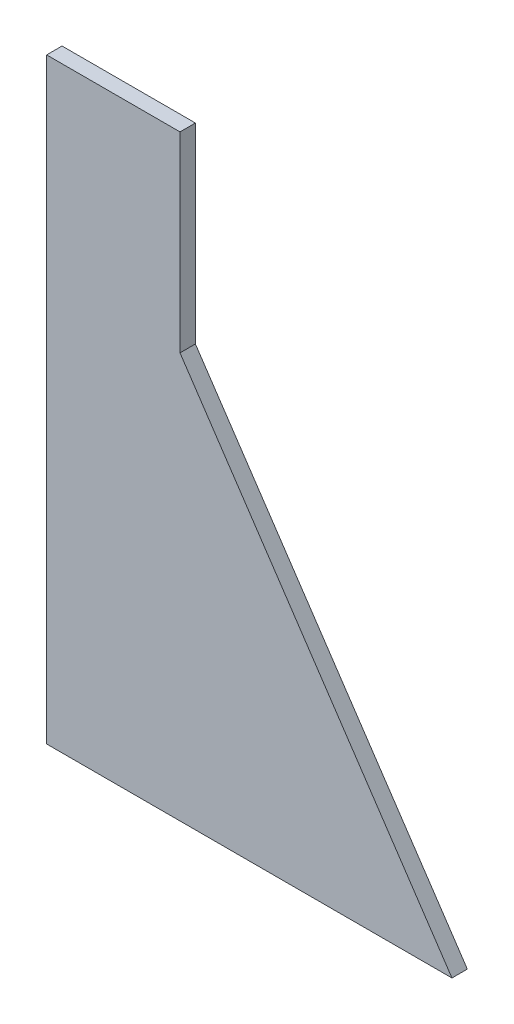
SolidWorks part; units mm, degrees
ref_plane "Front Plane" through (0, 0, 0) normal (0, 0, 1) x (1, 0, 0)
ref_plane "Top Plane" through (0, 0, 0) normal (0, 1, 0) x (1, 0, 0)
ref_plane "Right Plane" through (0, 0, 0) normal (1, 0, 0) x (0, 0, -1)
ref_plane "Plane1" through (0, 0, -231.834) normal (0, 0, -1) x (0, -1, 0)
sketch "Sketch1" plane through (0, 0, -231.834) normal (0, 0, 1) x (1, 0, 0)
  line L0 (0, 0) -> (0, -116.3532)
  line L1 (0, 0) -> (26, 0)
  line L2 (26, 0) -> (26, -37.3131)
  line L3 (26, -37.3131) -> (79.0188, -116.3532)
  line L4 (79.0188, -116.3532) -> (0, -116.3532)
  dimension "D1" = 26
  dimension "D2" = 116.3532
  dimension "D3" = 79.0188
  dimension "D4" = 95.1753
extrude "Boss-Extrude1" add sketch "Sketch1" against normal blind 3
